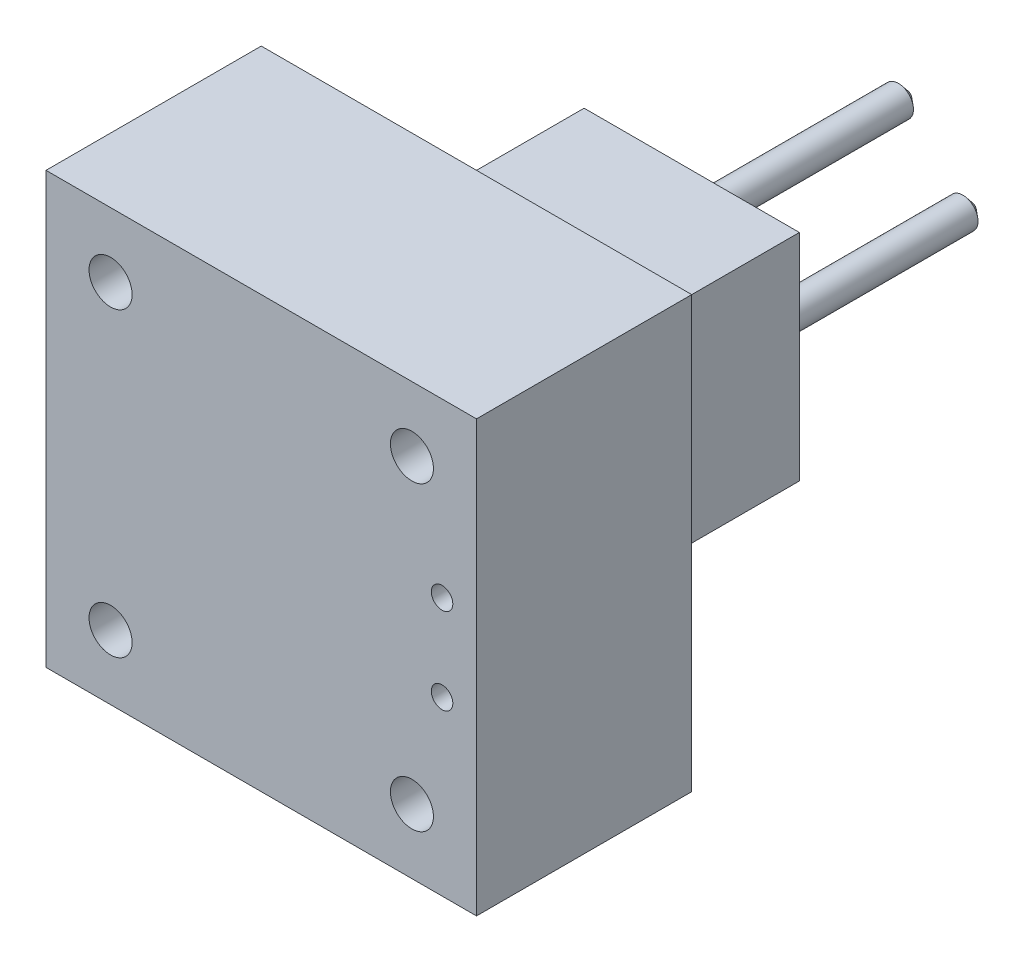
SolidWorks part; units mm, degrees
ref_plane "前视基准面" through (0, 0, 0) normal (0, 0, 1) x (1, 0, 0)
ref_plane "上视基准面" through (0, 0, 0) normal (0, 1, 0) x (1, 0, 0)
ref_plane "右视基准面" through (0, 0, 0) normal (1, 0, 0) x (0, 0, -1)
sketch "草图1" plane through (0, 0, 0) normal (0, 0, 1) x (1, 0, 0)
  line L1 (-46.0317, 31.2169) -> (53.9683, 31.2169)
  line L2 (-46.0317, 31.2169) -> (-46.0317, -68.7831)
  line L3 (-46.0317, -68.7831) -> (53.9683, -68.7831)
  line L4 (53.9683, 31.2169) -> (53.9683, -68.7831)
  dimension "D1" = 100
  dimension "D2" = 100
extrude "凸台-拉伸1" add sketch "草图1" along normal blind 50
sketch "草图2" plane through (0, 0, 0) normal (0, 0, -1) x (-1, 0, 0)
  line L0 (-53.9683, -68.7831) -> (-53.9683, 31.2169) construction
  line L1 (-53.9683, 31.2169) -> (46.0317, 31.2169) construction
  line L2 (46.0317, -68.7831) -> (-53.9683, -68.7831) construction
  line L3 (46.0317, 31.2169) -> (46.0317, -68.7831) construction
  circle A0 centre (-38.9683, 16.2169) radius 5
  circle A1 centre (31.0317, 16.2169) radius 5
  circle A2 centre (-38.9683, -53.7831) radius 5
  circle A3 centre (31.0317, -53.7831) radius 5
  point P10 (0, 0)
  point P12 (-32.847, 19.3827)
  point P16 (0, 0)
  point P17 (0, 0)
  dimension "D1" = 10
  dimension "D2" = 15
  dimension "D4" = 10
  dimension "D5" = 15
  dimension "D11" = 10
  dimension "D3" = 15
  dimension "D6" = 15
  dimension "D7" = 15
  dimension "D8" = 15
  dimension "D9" = 15
  dimension "D10" = 15
extrude "切除-拉伸1" cut sketch "草图2" against normal through all
sketch "草图3" plane through (0, 0, 0) normal (0, 0, -1) x (-1, 0, 0)
  line L0 (-53.9683, -68.7831) -> (-53.9683, 31.2169) construction
  line L1 (-53.9683, 31.2169) -> (46.0317, 31.2169) construction
  line L2 (46.0317, -68.7831) -> (-53.9683, -68.7831) construction
  circle A0 centre (-3.9683, -3.7831) radius 3.5
  circle A1 centre (-18.9683, -18.7831) radius 3.5
  circle A2 centre (-3.9683, -33.7831) radius 3.5
  circle A3 centre (11.0317, -18.7831) radius 3.5
  point P8 (0, 0)
  point P9 (0, 0)
  point P14 (0, 0)
  point P15 (0, 0)
  point P16 (0, 0)
  dimension "D1" = 7
  dimension "D2" = 50
  dimension "D3" = 35
  dimension "D4" = 15
  dimension "D7" = 35
  dimension "D5" = 15
  dimension "D6" = 50
  dimension "D8" = 15
  dimension "D9" = 15
sketch "草图4" plane through (0, 0, 0) normal (0, 0, -1) x (-1, 0, 0)
  line L0 (-53.9683, -68.7831) -> (-53.9683, 31.2169) construction
  line L1 (-53.9683, 31.2169) -> (46.0317, 31.2169) construction
  line L2 (46.0317, -68.7831) -> (-53.9683, -68.7831) construction
  circle A0 centre (-45.9683, -8.7831) radius 2.5
  circle A1 centre (-45.9683, -28.7831) radius 2.5
  dimension "D1" = 5
  dimension "D2" = 5
  dimension "D3" = 8
  dimension "D4" = 8
  dimension "D5" = 40
  dimension "D6" = 40
extrude "切除-拉伸2" cut sketch "草图4" against normal through all
sketch "草图5" plane through (0, 0, 0) normal (0, 0, -1) x (-1, 0, 0)
  line L0 (46.0317, 31.2169) -> (46.0317, -68.7831) construction
  line L1 (-28.9683, 6.2169) -> (21.0317, 6.2169)
  line L2 (-28.9683, 6.2169) -> (-28.9683, -43.7831)
  line L3 (-28.9683, -43.7831) -> (21.0317, -43.7831)
  line L4 (21.0317, 6.2169) -> (21.0317, -43.7831)
  line L5 (-53.9683, 31.2169) -> (46.0317, 31.2169) construction
  dimension "D1" = 50
  dimension "D2" = 50
  dimension "D3" = 25
  dimension "D4" = 25
extrude "凸台-拉伸3" add sketch "草图5" along normal blind 50
extrude "凸台-拉伸4" add sketch "草图3" along normal blind 100
chamfer "倒角4" distance 2 angle 50 4 edges at (0.4683, -3.7831, -100) (-14.5317, -18.7831, -100) (0.4683, -33.7831, -100) (15.4683, -18.7831, -100)
